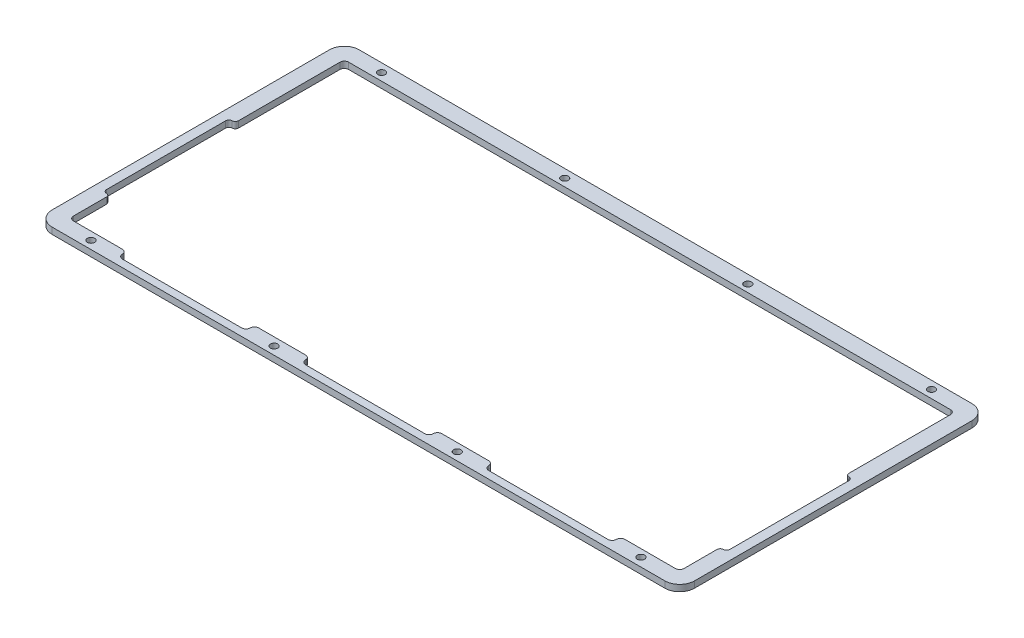
SolidWorks part; units mm, degrees
ref_plane "Front Plane" through (0, 0, 0) normal (0, 0, 1) x (1, 0, 0)
ref_plane "Top Plane" through (0, 0, 0) normal (0, 1, 0) x (1, 0, 0)
ref_plane "Right Plane" through (0, 0, 0) normal (1, 0, 0) x (0, 0, -1)
sketch "Sketch1" plane through (0, 0, 0) normal (0, 1, 0) x (1, 0, 0)
  line L1 (0, 0) -> (350, 0)
  line L2 (0, 0) -> (0, 200)
  line L3 (0, 200) -> (350, 200)
  line L4 (350, 0) -> (350, 200)
extrude "Boss-Extrude1" add sketch "Sketch1" along normal blind 3
sketch "Sketch2" plane through (0, 3, 0) normal (0, 1, 0) x (1, 0, 0)
  line L0 (48.2817, 9.1942) -> (104.2817, 9.1942)
  line L1 (108.2817, 13.1942) -> (130.2817, 13.1942)
  line L2 (134.2817, 9.1942) -> (190.2817, 9.1942)
  line L3 (194.2817, 13.1942) -> (216.2817, 13.1942)
  line L4 (220.2817, 9.1942) -> (276.2817, 9.1942)
  line L5 (16.2817, 33.6942) -> (16.2817, 89.6942)
  line L6 (21.2817, 142.3937) -> (303.9811, 142.3937)
  line L7 (11.7817, 12.6942) -> (11.7817, 142.8937)
  line L8 (306.4811, 5.6942) -> (18.7817, 5.6942)
  line L9 (313.4811, 142.8937) -> (313.4811, 12.6942)
  line L10 (18.7817, 149.8937) -> (306.4811, 149.8937)
  line L11 (308.9811, 33.6942) -> (308.9811, 89.6942)
  line L12 (19.2817, 92.6942) -> (19.2817, 140.3937)
  line L13 (21.2817, 142.3937) -> (303.9811, 142.3937)
  line L14 (305.9811, 92.6942) -> (305.9811, 140.3937)
  line L15 (280.2817, 13.1942) -> (303.9811, 13.1942)
  line L16 (305.9811, 15.1942) -> (305.9811, 30.6942)
  line L17 (21.2817, 13.1942) -> (44.2817, 13.1942)
  line L18 (19.2817, 15.1942) -> (19.2817, 30.6942)
  arc A0 (46.2817, 11.1942) -> (44.2817, 13.1942) centre (44.2817, 11.1942) ccw
  arc A1 (46.2817, 11.1942) -> (48.2817, 9.1942) centre (48.2817, 11.1942) ccw
  arc A2 (104.2817, 9.1942) -> (106.2817, 11.1942) centre (104.2817, 11.1942) ccw
  arc A3 (108.2817, 13.1942) -> (106.2817, 11.1942) centre (108.2817, 11.1942) ccw
  arc A4 (132.2817, 11.1942) -> (130.2817, 13.1942) centre (130.2817, 11.1942) ccw
  arc A5 (132.2817, 11.1942) -> (134.2817, 9.1942) centre (134.2817, 11.1942) ccw
  arc A6 (190.2817, 9.1942) -> (192.2817, 11.1942) centre (190.2817, 11.1942) ccw
  arc A7 (194.2817, 13.1942) -> (192.2817, 11.1942) centre (194.2817, 11.1942) ccw
  arc A8 (218.2817, 11.1942) -> (216.2817, 13.1942) centre (216.2817, 11.1942) ccw
  arc A9 (218.2817, 11.1942) -> (220.2817, 9.1942) centre (220.2817, 11.1942) ccw
  arc A10 (276.2817, 9.1942) -> (278.2817, 11.1942) centre (276.2817, 11.1942) ccw
  arc A11 (280.2817, 13.1942) -> (278.2817, 11.1942) centre (280.2817, 11.1942) ccw
  arc A12 (19.2817, 30.6942) -> (17.7817, 32.1942) centre (17.7817, 30.6942) ccw
  arc A13 (16.2817, 33.6942) -> (17.7817, 32.1942) centre (17.7817, 33.6942) ccw
  arc A14 (17.7817, 91.1942) -> (16.2817, 89.6942) centre (17.7817, 89.6942) ccw
  arc A15 (17.7817, 91.1942) -> (19.2817, 92.6942) centre (17.7817, 92.6942) ccw
  circle A16 centre (291.2817, 9.6942) radius 1.7
  circle A17 centre (205.2817, 9.4442) radius 1.7
  circle A18 centre (33.2817, 9.4442) radius 1.7
  circle A19 centre (119.2817, 9.4442) radius 1.7
  circle A20 centre (291.2817, 146.1437) radius 1.7
  circle A21 centre (205.2817, 145.8937) radius 1.7
  circle A22 centre (33.2817, 145.8937) radius 1.7
  circle A23 centre (119.2817, 145.8937) radius 1.7
  arc A24 (18.7817, 149.8937) -> (11.7817, 142.8937) centre (18.7817, 142.8937) ccw
  arc A25 (11.7817, 12.6942) -> (18.7817, 5.6942) centre (18.7817, 12.6942) ccw
  arc A26 (306.4811, 5.6942) -> (313.4811, 12.6942) centre (306.4811, 12.6942) ccw
  arc A27 (313.4811, 142.8937) -> (306.4811, 149.8937) centre (306.4811, 142.8937) ccw
  arc A28 (307.4811, 32.1942) -> (305.9811, 30.6942) centre (307.4811, 30.6942) ccw
  arc A29 (307.4811, 32.1942) -> (308.9811, 33.6942) centre (307.4811, 33.6942) ccw
  arc A30 (308.9811, 89.6942) -> (307.4811, 91.1942) centre (307.4811, 89.6942) ccw
  arc A31 (305.9811, 92.6942) -> (307.4811, 91.1942) centre (307.4811, 92.6942) ccw
  arc A32 (21.2817, 142.3937) -> (19.2817, 140.3937) centre (21.2817, 140.3937) ccw
  arc A33 (305.9811, 140.3937) -> (303.9811, 142.3937) centre (303.9811, 140.3937) ccw
  arc A34 (303.9811, 13.1942) -> (305.9811, 15.1942) centre (303.9811, 15.1942) ccw
  arc A35 (19.2817, 15.1942) -> (21.2817, 13.1942) centre (21.2817, 15.1942) ccw
extrude "Cut-Extrude2" cut sketch "Sketch2" against normal blind 3 contours L18 A35 L17 A0 A1 L0 A2 A3 L1 A4 A5 L2 A6 A7 L3 A8 A9 L4 A10 A11 L15 A34 L16 A28 A29 L11 A30 A31 L14 A33 L6 A32 L12 A15 A14 L5 A13 A12 | L3 L0 L1 L2 A27 L9 A26 L8 A25 L7 A24 L10 | A20 | A21 | A22 | A23 | A18 | A19 | A17 | A16
